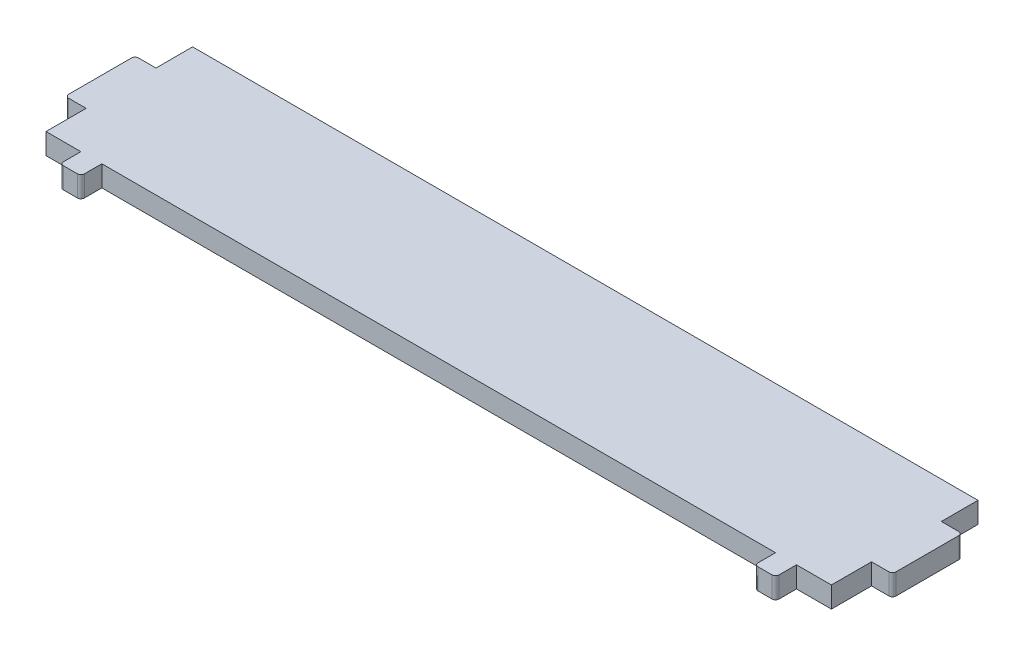
SolidWorks part; units mm, degrees
ref_plane "Спереди" through (0, 0, 0) normal (0, 0, 1) x (1, 0, 0)
ref_plane "Сверху" through (0, 0, 0) normal (0, 1, 0) x (1, 0, 0)
ref_plane "Справа" through (0, 0, 0) normal (1, 0, 0) x (0, 0, -1)
sketch "Эскиз1" plane through (0, 0, 0) normal (0, 1, 0) x (1, 0, 0)
  line L0 (0, -21) -> (0, 21.8864) construction
  line L1 (-56.25, -21) -> (56.25, -21)
  line L2 (56.25, -21) -> (56.25, -15.25)
  line L5 (56.25, -15.25) -> (59.25, -15.25)
  line L6 (59.25, -15.25) -> (59.25, -5.25)
  line L7 (59.25, -5.25) -> (56.25, -5.25)
  line L8 (56.25, -5.25) -> (56.25, 0)
  line L9 (56.25, 0) -> (-56.25, 0)
  line L10 (-56.25, -5.25) -> (-56.25, 0)
  line L11 (-59.25, -5.25) -> (-56.25, -5.25)
  line L12 (-59.25, -15.25) -> (-59.25, -5.25)
  line L13 (-56.25, -15.25) -> (-59.25, -15.25)
  line L16 (-56.25, -21) -> (-56.25, -15.25)
  line L17 (-48.25, -21) -> (-51.25, -24) construction
  line L18 (48.25, -24) -> (51.25, -24)
  line L19 (48.25, -24) -> (48.25, -21)
  line L20 (48.25, -21) -> (51.25, -21)
  line L21 (51.25, -24) -> (51.25, -21)
  line L22 (48.25, -24) -> (51.25, -21) construction
  line L23 (48.25, -21) -> (51.25, -24) construction
  line L24 (-48.25, -24) -> (-51.25, -21) construction
  line L25 (-51.25, -24) -> (-51.25, -21)
  line L26 (-48.25, -21) -> (-51.25, -21)
  line L27 (-48.25, -24) -> (-48.25, -21)
  line L28 (-48.25, -24) -> (-51.25, -24)
  point P3 (49.75, -22.5)
  point P13 (57.75, -5.25)
  point P14 (50, -9.6)
  point P18 (0, 0)
  point P25 (-50, -9.6)
  point P28 (-49.75, -22.5)
  dimension "D5" = 3
  dimension "D1" = 3
  dimension "D2" = 10
  dimension "D3" = 6.25
  dimension "D4" = 21
  dimension "D6" = 5.25
  dimension "D7" = 100
  dimension "D8" = 5
  dimension "D9" = 9.6
extrude "Бобышка-Вытянуть1" add sketch "Эскиз1" along normal blind 3
fillet "Скругление1" radius 0.5 8 edges at (-59.25, 1.5, 5.25) (-59.25, 1.5, 15.25) (59.25, 1.5, 5.25) (59.25, 1.5, 15.25) (-51.25, 1.5, 24) (-48.25, 1.5, 24) (48.25, 1.5, 24) (51.25, 1.5, 24)
